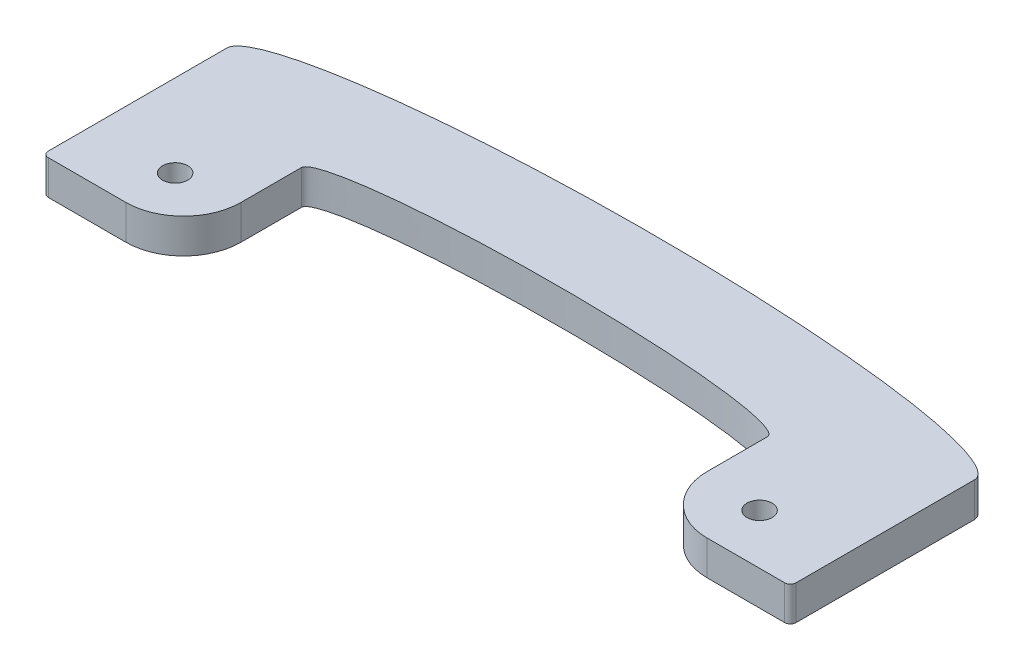
SolidWorks part; units mm, degrees
ref_plane "Front Plane" through (0, 0, 0) normal (0, 0, 1) x (1, 0, 0)
ref_plane "Top Plane" through (0, 0, 0) normal (0, 1, 0) x (1, 0, 0)
ref_plane "Right Plane" through (0, 0, 0) normal (1, 0, 0) x (0, 0, -1)
sketch "Sketch1" plane through (0, 0, 0) normal (0, 1, 0) x (1, 0, 0)
  line L0 (0, 0) -> (-32.5, 0)
  line L1 (-32.5, 0) -> (-32.5, 16)
  line L3 (0, 16) -> (0, 0)
  line L4 (0, 16) -> (0, 20.5)
  ellipse E0 centre (0, 16) end of major axis (-32.5, 16) minor radius 4.5 (0, 20.5) -> (-32.5, 16) ccw
  dimension "D1" = 4.5
  dimension "D2" = 32.5
  dimension "D3" = 16
extrude "Boss-Extrude1" add sketch "Sketch1" along normal blind 3
mirror "Mirror1" about plane through (0, 3, -16) normal (-1, 0, 0) of "Boss-Extrude1"
sketch "Sketch2" plane through (0, 3, 0) normal (0, 1, 0) x (1, 0, 0)
  line L0 (20.26, 10.25) -> (20.26, 0)
  line L1 (-20.26, 10.25) -> (-20.26, 0)
  line L2 (-32.5, 0) -> (32.5, 0) construction
  line L3 (-20.26, 0) -> (20.26, 0)
  line L4 (0, 0) -> (0, 10.25)
  line L5 (0, 10.25) -> (0, 12.5)
  line L6 (-32.5, 16) -> (-32.5, 0) construction
  line L7 (0, 12.5) -> (0, 20.5) construction
  ellipse E0 centre (0, 10.25) end of major axis (-20.26, 10.25) minor radius 2.25 (20.26, 10.25) -> (-20.26, 10.25) ccw
  ellipse E2 centre (0, 16) end of major axis (-32.5, 16) minor radius 4.5 (32.5, 16) -> (-32.5, 16) ccw construction
  line M1 (-32.5, 0) -> (32.5, 0)
  dimension "D1" = 2.25
  dimension "D2" = 12.24
  dimension "D3" = 8
extrude "Cut-Extrude1" cut sketch "Sketch2" against normal through all contours L5 E0 L1 L4 M1 | L0 E0 L5 L4 L3
sketch "Sketch3" plane through (0, 0, 0) normal (0, -1, 0) x (1, 0, 0)
  circle A0 centre (25.46, -4.3615) radius 1.0922 construction
  circle A1 centre (-25.34, -4.3615) radius 1.0922 construction
  circle A2 centre (25.46, -4.3615) radius 1.0922
  circle A3 centre (-25.34, -4.3615) radius 1.0922
extrude "Cut-Extrude2" cut sketch "Sketch3" against normal through all
fillet "Fillet1" radius 5 2 edges at (-20.26, 1.5, 0) (20.26, 1.5, 0)
fillet "Fillet2" radius 0.5 2 edges at (32.5, 1.5, 0) (-32.5, 1.5, 0)
